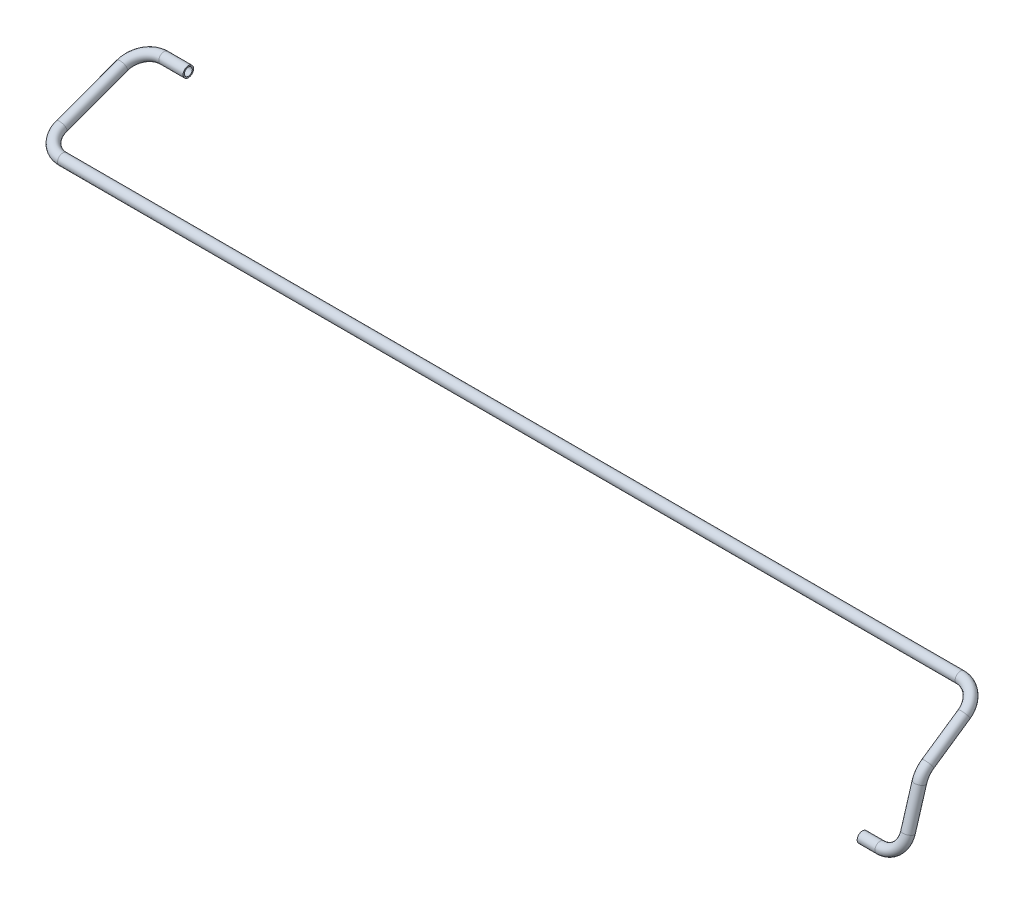
SolidWorks part; units mm, degrees
ref_plane "Plane1" through (0, 0, 0) normal (0, 0, 1) x (1, 0, 0)
ref_plane "Plane2" through (0, 0, 0) normal (0, 1, 0) x (1, 0, 0)
ref_plane "Plane3" through (0, 0, 0) normal (1, 0, 0) x (0, 0, -1)
sketch3d "3DSketch1"
  line L0 (0, 0, 0) -> (27, 0, 0)
  line L1 (60, 0, 0) -> (60, 100, 0) construction
  line L2 (60, 100, 0) -> (60, 100, -30) construction
  line L3 (60, 31.6083, -9.4825) -> (60, 88.8386, -26.6516)
  line L4 (60, 100, -30) -> (60, 163, -30) construction
  line L5 (60, 163, -30) -> (60, 163, -122) construction
  line L6 (60, 106.5839, -39.6147) -> (60, 144.3548, -94.7721)
  line L7 (27, 163, -122) -> (-1338.5, 163, -122)
  line L8 (-1371.5, 163, -122) -> (-1371.5, 193, -122) construction
  line L9 (-1371.5, 193, -122) -> (-1371.5, 193, -276) construction
  line L10 (-1371.5, 174.3663, -152.9808) -> (-1371.5, 208.1337, -245.0192)
  line L12 (-1371.5, 193, -276) -> (-1371.5, 219.5, -276) construction
  line L14 (-1338.5, 219.5, -276) -> (-1301.5, 219.5, -276)
  arc A0 (27, 0, 0) -> (60, 31.6083, -9.4825) centre (27, 31.6083, -9.4825) ccw
  arc A1 (60, 106.5839, -39.6147) -> (60, 88.8386, -26.6516) centre (60, 79.3561, -58.2598) ccw
  arc A2 (27, 163, -122) -> (60, 144.3548, -94.7721) centre (27, 144.3548, -94.7721) ccw
  arc A3 (-1338.5, 163, -122) -> (-1371.5, 174.3663, -152.9808) centre (-1338.5, 174.3663, -152.9808) ccw
  arc A5 (-1338.5, 219.5, -276) -> (-1371.5, 208.1337, -245.0192) centre (-1338.5, 208.1337, -245.0192) ccw
  point P10 (60, 0, 0)
  point P12 (27, 41.0907, 22.1258)
  point P15 (60, 100, -30)
  point P17 (93, 79.3561, -58.2598)
  point P20 (60, 163, -122)
  point P22 (27, 117.1269, -113.4173)
  point P24 (-1371.5, 219.5, -276)
  point P30 (-1371.5, 163, -122)
  point P32 (-1338.5, 143.3856, -164.3471)
  point P40 (-1371.5, 219.5, -276)
  point P42 (-1338.5, 239.1144, -233.6529)
  dimension "D6" = 33
  dimension "D7" = 33
  dimension "D8" = 33
  dimension "D15" = 33
  dimension "D17" = 33
  dimension "D1" = 60
  dimension "D2" = 100
  dimension "D3" = 30
  dimension "D4" = 1431.5
  dimension "D10" = 70
  dimension "D5" = 92
  dimension "D9" = 63
  dimension "D11" = 30
  dimension "D12" = 154
  dimension "D14" = 26.5
ref_plane "Plane4" through (0, 0, 0) normal (1, 0, 0) x (0, 0, -1)
sketch "Sketch1" plane through (0, 0, 0) normal (1, 0, 0) x (0, 0, -1)
  circle A0 centre (0, 0) radius 8
  circle A1 centre (0, 0) radius 6
  dimension "D1" = 12
  dimension "D2" = 16
sweep "Sweep1" add profiles "Sketch1" path "3DSketch1"
